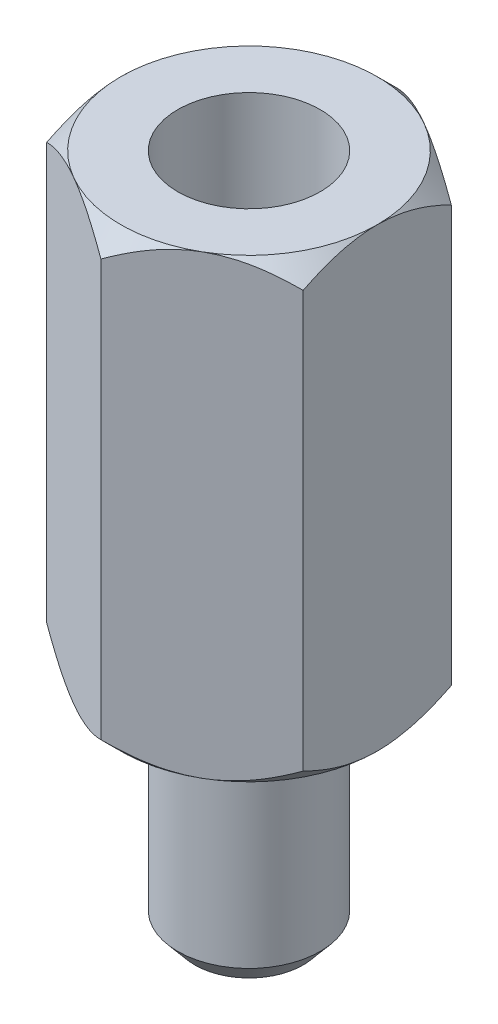
SolidWorks part; units mm, degrees
ref_plane "Front Plane" through (0, 0, 0) normal (0, 0, 1) x (1, 0, 0)
ref_plane "Top Plane" through (0, 0, 0) normal (0, 1, 0) x (1, 0, 0)
ref_plane "Right Plane" through (0, 0, 0) normal (1, 0, 0) x (0, 0, -1)
sketch "Sketch2" plane through (0, 0, 0) normal (0, 1, 0) x (1, 0, 0)
  circle A0 centre (0, 0) radius 1.25
  dimension "D1" = 2.5
extrude "Boss-Extrude1" add sketch "Sketch2" along normal blind 3.9
sketch "Sketch3" plane through (0, 3.9, 0) normal (0, 1, 0) x (1, 0, 0)
  line L1 (0, -2.5981) -> (2.25, -1.299)
  line L2 (2.25, -1.299) -> (2.25, 1.299)
  line L3 (2.25, 1.299) -> (0, 2.5981)
  line L4 (0, 2.5981) -> (-2.25, 1.299)
  line L5 (-2.25, 1.299) -> (-2.25, -1.299)
  line L6 (-2.25, -1.299) -> (0, -2.5981)
  circle A0 centre (0, 0) radius 2.25 construction
  dimension "D1" = 4.5
extrude "Boss-Extrude2" add sketch "Sketch3" along normal blind 8
sketch "Sketch4" plane through (0, 11.9, 0) normal (0, 1, 0) x (1, 0, 0)
  circle A0 centre (0, 0) radius 1.25
  dimension "D1" = 2.5
extrude "Cut-Extrude1" cut sketch "Sketch4" against normal blind 4.8
sketch "Sketch5" plane through (0, 11.9, 0) normal (0, 1, 0) x (1, 0, 0)
  circle A0 centre (0, 0) radius 2.25
extrude "Cut-Extrude4" cut sketch "Sketch5" against normal through all draft 45 flip side to cut
sketch "Sketch6" plane through (0, 3.9, 0) normal (0, -1, 0) x (1, 0, 0)
  circle A0 centre (0, 0) radius 2.25
extrude "Cut-Extrude5" cut sketch "Sketch6" against normal through all draft 45 flip side to cut
chamfer "Chamfer1" distance 0.3 angle 50 1 edges at (0, 0, 1.25)
